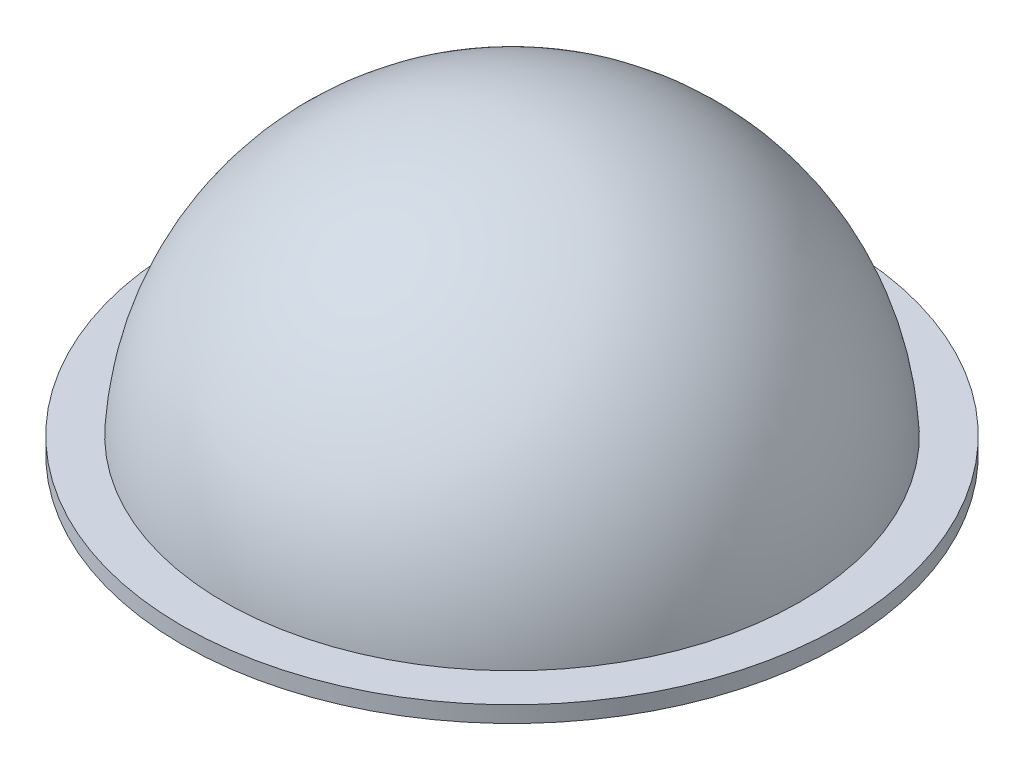
SolidWorks part; units mm, degrees
ref_plane "Front" through (0, 0, 0) normal (0, 0, 1) x (1, 0, 0)
ref_plane "Top" through (0, 0, 0) normal (0, 1, 0) x (1, 0, 0)
ref_plane "Right" through (0, 0, 0) normal (1, 0, 0) x (0, 0, -1)
sketch "Sketch1" plane through (0, 0, 0) normal (0, 0, 1) x (1, 0, 0)
  line L2 (-101.6, 0) -> (-101.6, 5)
  line L3 (-101.6, 5) -> (-88.7593, 5)
  line L8 (0, 0) -> (0, 88.9) construction
  line L9 (0, 88.9) -> (0, 85.725)
  line L10 (-101.6, 0) -> (88.9, 0) construction
  line L11 (-101.6, 0) -> (-85.725, 0)
  arc A0 (88.9, 0) -> (-88.9, 0) centre (0, 0) ccw construction
  arc A1 (0, 85.725) -> (-85.725, 0) centre (0, 0) ccw
  arc A2 (-88.7593, 5) -> (0, 88.9) centre (0, 0) cw
  dimension "D1" = 177.8
  dimension "D2" = 171.45
  dimension "D3" = 12.7
  dimension "D6" = 5
revolve "Revolve1" add sketch "Sketch1" angle 360 about L8
